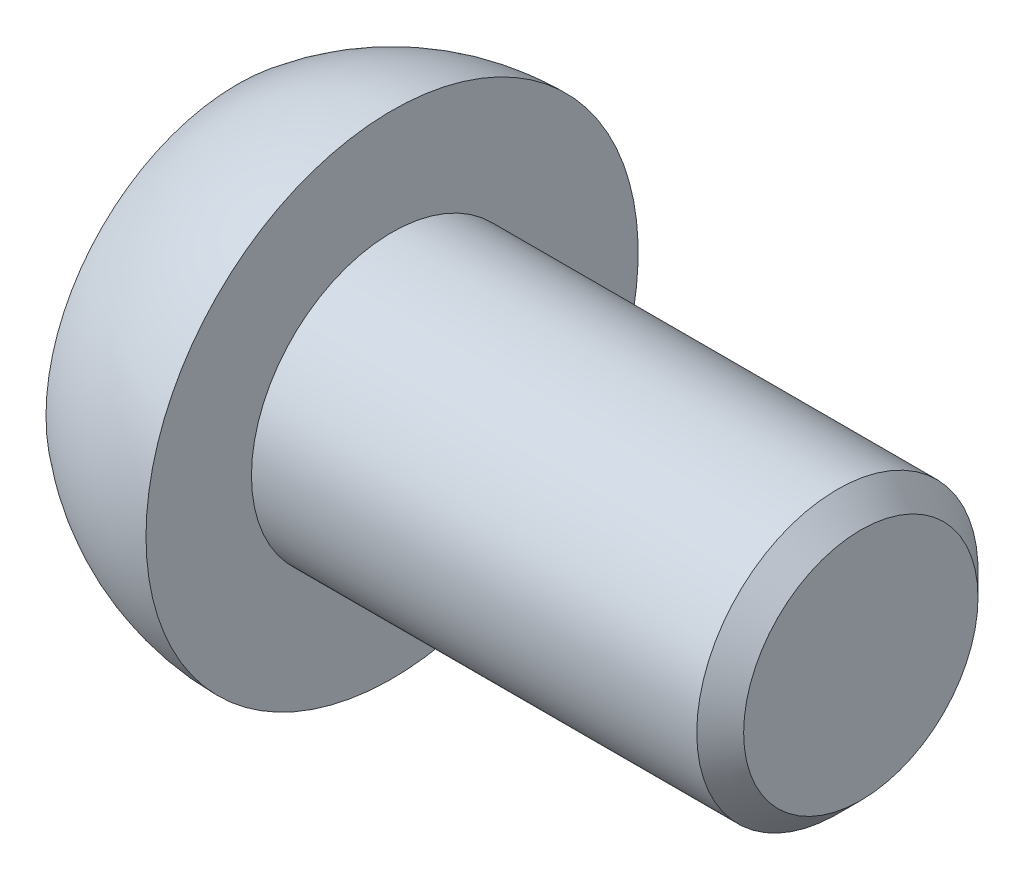
SolidWorks part; units mm, degrees
material "AISI 1020"
ref_plane "Спереди" through (0, 0, 0) normal (0, 0, 1) x (1, 0, 0)
ref_plane "Сверху" through (0, 0, 0) normal (0, 1, 0) x (1, 0, 0)
ref_plane "Справа" through (0, 0, 0) normal (1, 0, 0) x (0, 0, -1)
sketch "Эскиз1" plane through (0, 0, 0) normal (0, 0, 1) x (1, 0, 0)
  line L0 (-165.7494, 0) -> (8121.7194, 0) construction
  line L1 (0, 5.25) -> (0, 3)
  line L2 (0, 3) -> (10, 3)
  line L3 (10, 3) -> (10, 0)
  line L4 (-3.3, 0) -> (-3.3, 4.0832)
  line L5 (10, 0) -> (-3.3, 0)
  arc A0 (0, 5.25) -> (-3.3, 4.0832) centre (0, 0) ccw
  dimension "D1" = 6
  dimension "D2" = 10
  dimension "D3" = 10.5
  dimension "D4" = 3.3
revolve "Повернуть1" add sketch "Эскиз1" angle 360 about L0
cosmetic thread "Условное изображение резьбы1" parameters "D2"=4.891
sketch "Эскиз2" plane through (-3.3, 0, 0) normal (-1, 0, 0) x (0, 0, 1)
  line L1 (0, -2.3094) -> (2, -1.1547)
  line L2 (2, -1.1547) -> (2, 1.1547)
  line L3 (2, 1.1547) -> (0, 2.3094)
  line L4 (0, 2.3094) -> (-2, 1.1547)
  line L5 (-2, 1.1547) -> (-2, -1.1547)
  line L6 (-2, -1.1547) -> (0, -2.3094)
  circle A0 centre (0, 0) radius 2 construction
  dimension "D1" = 4
extrude "Вырез-Вытянуть1" cut sketch "Эскиз2" against normal blind 3
fillet "Скругление1" radius 0.25 6 edges at (-3.3, -1.7321, -1) (-3.3, -1.7321, 1) (-3.3, 0, 2) (-3.3, 1.7321, 1) (-3.3, 1.7321, -1) (-3.3, 0, -2)
chamfer "Фаска1" distance 0.5 angle 45 1 edges at (10, 0, 3)
